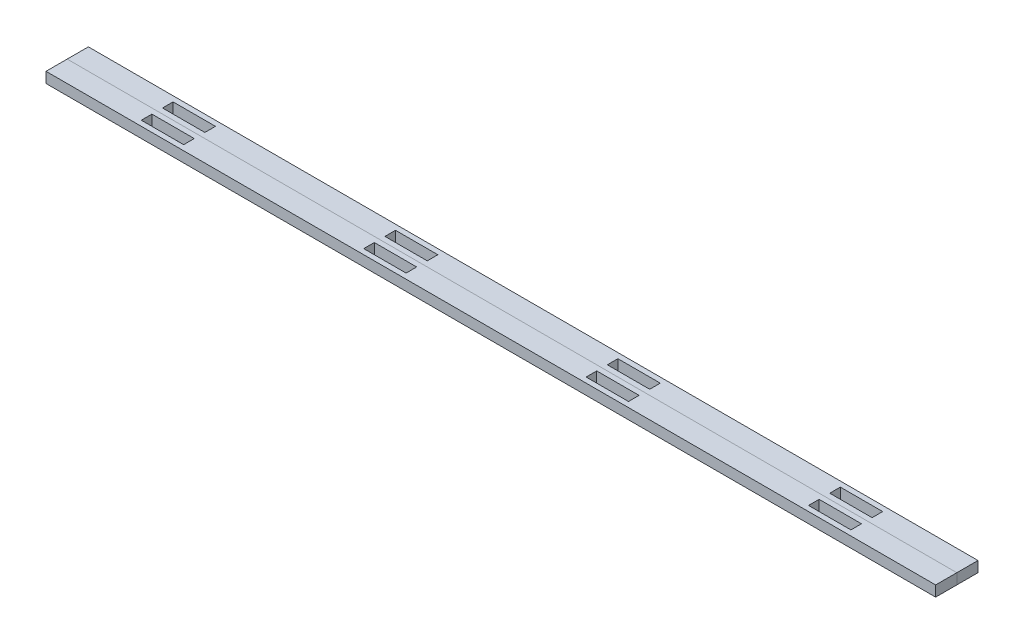
SolidWorks part; units mm, degrees
material "Cedar"
ref_plane "Front Plane" through (0, 0, 0) normal (0, 0, 1) x (1, 0, 0)
ref_plane "Top Plane" through (0, 0, 0) normal (0, 1, 0) x (1, 0, 0)
ref_plane "Right Plane" through (0, 0, 0) normal (1, 0, 0) x (0, 0, -1)
sketch "Sketch1" plane through (0, 0, 0) normal (0, 1, 0) x (1, 0, 0)
  line L1 (-266.7, 6.35) -> (266.7, 6.35)
  line L2 (-266.7, 6.35) -> (-266.7, -6.35)
  line L3 (-266.7, -6.35) -> (266.7, -6.35)
  line L4 (266.7, 6.35) -> (266.7, -6.35)
  line L5 (-266.7, 6.35) -> (266.7, -6.35) construction
  line L6 (-266.7, -6.35) -> (266.7, 6.35) construction
  point P0 (0, 0)
  dimension "D1" = 533.4
  dimension "D2" = 12.7
extrude "Boss-Extrude1" add sketch "Sketch1" along normal blind 6.35
sketch "Sketch2" plane through (0, 6.35, 0) normal (0, 1, 0) x (1, 0, 0)
  line L0 (-266.7, 0) -> (-212.725, 0) construction
  line L1 (-212.725, 3.175) -> (-187.325, 3.175)
  line L2 (-212.725, 3.175) -> (-212.725, -3.175)
  line L3 (-212.725, -3.175) -> (-187.325, -3.175)
  line L4 (-187.325, 3.175) -> (-187.325, -3.175)
  line L5 (-212.725, 3.175) -> (-187.325, -3.175) construction
  line L6 (-212.725, -3.175) -> (-187.325, 3.175) construction
  line L7 (-266.7, 6.35) -> (-266.7, -6.35) construction
  point P0 (-200.025, 0)
  dimension "D1" = 25.4
  dimension "D2" = 6.35
  dimension "D3" = 53.975
extrude "Cut-Extrude1" cut sketch "Sketch2" against normal through all
pattern_linear "LPattern1" count 4 spacing 133.35 along (1, 0, 0) of "Cut-Extrude1"
pattern_linear "LPattern2" count 2 spacing 12.7 along (0, 0, 1) of bodies 103
